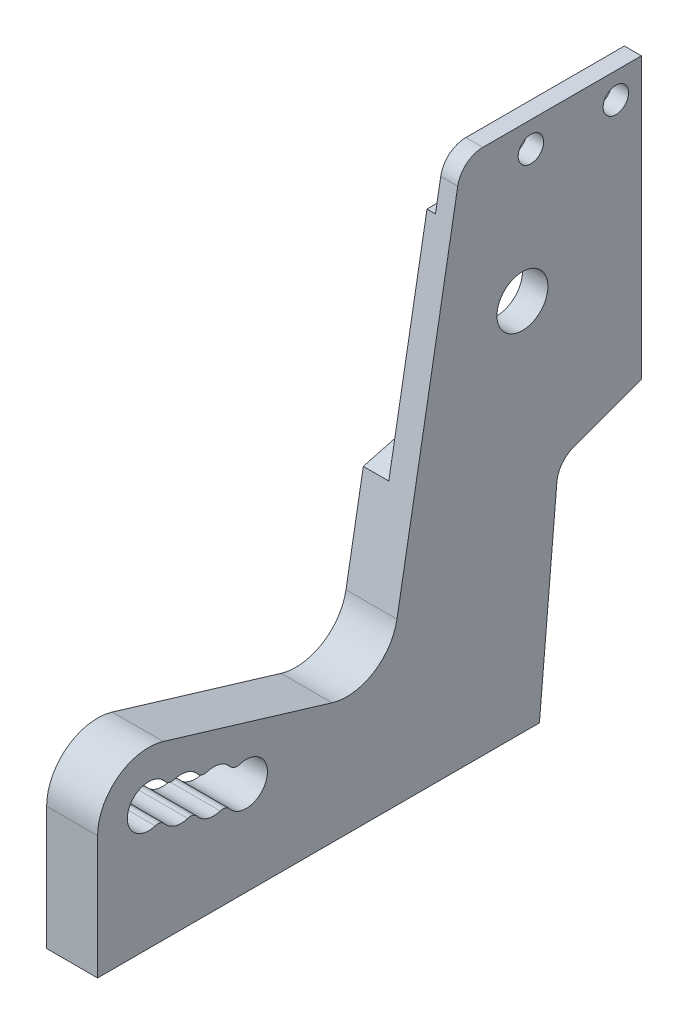
SolidWorks part; units mm, degrees
material "1060 Alloy"
ref_plane "Front Plane" through (0, 0, 0) normal (0, 0, 1) x (1, 0, 0)
ref_plane "Top Plane" through (0, 0, 0) normal (0, 1, 0) x (1, 0, 0)
ref_plane "Right Plane" through (0, 0, 0) normal (1, 0, 0) x (0, 0, -1)
sketch "Sketch1" plane through (0, 0, 0) normal (1, 0, 0) x (0, 0, -1)
  line L1 (0, 0) -> (64, 0)
  line L2 (0, 0) -> (0, 62)
  line L3 (0, 62) -> (64, 62)
  line L4 (64, 0) -> (64, 62)
  circle A0 centre (6, 14.5) radius 2.5
  circle A1 centre (50, 44) radius 3
  dimension "D1" = 6
  dimension "D2" = 5
  dimension "D3" = 14.5
  dimension "D4" = 6
  dimension "D5" = 44
  dimension "D6" = 50
  dimension "D7" = 64
  dimension "D8" = 62
extrude "Boss-Extrude1" add sketch "Sketch1" along normal blind 6
sketch "Sketch2" plane through (6, 0, 0) normal (1, 0, 0) x (0, 0, -1)
  line L0 (0, 62) -> (0, 0) construction
  line L1 (0, 0) -> (64, 0) construction
  line L2 (7.7322, 20.2445) -> (27.5931, 14.2555)
  line L4 (0, 14.5) -> (0, 63)
  line L5 (0, 63) -> (43, 63)
  line L6 (43, 63) -> (35.2342, 18.9581)
  line L7 (64, 62) -> (0, 62) construction
  arc A0 (0, 14.5) -> (7.7322, 20.2445) centre (6, 14.5) cw
  circle A1 centre (50, 44) radius 5 construction
  circle A2 centre (6, 14.5) radius 2.5 construction
  arc A4 (27.5931, 14.2555) -> (35.2342, 18.9581) centre (29.3254, 20) ccw
  dimension "D2" = 10
  dimension "D4" = 80
  dimension "D1" = 1
  dimension "D3" = 43
  dimension "D5" = 20
extrude "Cut-Extrude1" cut sketch "Sketch2" against normal up to next
sketch "Sketch3" plane through (6, 0, 0) normal (1, 0, 0) x (0, 0, -1)
  line L2 (0, 0) -> (64, 0) construction
  line L57 (64, 0) -> (52, 0)
  line L58 (64, 0) -> (64, 29)
  line L59 (64, 29) -> (54.2259, 25.4425)
  line L60 (52, 0) -> (54.2259, 25.4425)
  dimension "D1" = 52
  dimension "D2" = 29
  dimension "D3" = 70
  dimension "D4" = 85
extrude "Cut-Extrude2" cut sketch "Sketch3" against normal up to next
fillet "Fillet1" radius 3 1 edges at (3, 62, -42.8237)
fillet "Fillet2" radius 3 1 edges at (3, 25.4425, -54.2259)
hole_wizard "Tap Drill for M3 Tap1" positions "Sketch5" profile "Sketch4" hole size "M3" standard "ISO"
sketch "Sketch5" plane through (0, 0, 0) normal (0, -1, 0) x (-1, 0, 0)
  line L1 (-6, 0) -> (0, 0) construction
  line L2 (-6, 0) -> (-6, 52) construction
  point P0 (-3, 48)
  point P2 (-3, 12)
  dimension "D1" = 3
  dimension "D2" = 12
  dimension "D3" = 36
sketch "Sketch4" plane through (3, 0, -48) normal (1, 0, 0) x (0, 0, -1)
  line L0 (0, 0) -> (0, 9.7511)
  line L1 (0, 9.7511) -> (1.25, 9)
  line L2 (1.25, 9) -> (1.25, 0)
  line L5 (1.25, 0) -> (0, 0)
  line L10 (0, 9.7511) -> (-1.25, 9) construction
  line L11 (0, -6.35) -> (0, 107.95) construction
  dimension "Hole Dia." = 2.5
  dimension "Hole Depth" = 9
  dimension "Drill Angle" = 118
sketch "Sketch9" plane through (0, 0, 0) normal (-1, 0, 0) x (0, 0, 1)
  line L0 (-64, 62) -> (-64, 35)
  line L1 (-64, 62) -> (-45.341, 62) construction
  line L3 (-64, 29) -> (-64, 62) construction
  line L4 (-64, 62) -> (-42.8237, 62)
  line L5 (-42.8237, 62) -> (-37.2725, 30.5179)
  line L6 (-54, 35) -> (-64, 35)
  line L11 (-35.2342, 18.9581) -> (-42.3865, 59.5209) construction
  line L12 (-37.2725, 30.5179) -> (-54, 35)
  dimension "D1" = 10
  dimension "D2" = 27
  dimension "D5" = 65
extrude "Cut-Extrude3" cut sketch "Sketch9" against normal blind 3
sketch "Sketch10" plane through (3, 0, 0) normal (-1, 0, 0) x (0, 0, 1)
  line L0 (-45.341, 62) -> (-64, 62) construction
  line L1 (-64, 62) -> (-64, 35) construction
  circle A0 centre (-61, 59) radius 1.5
  circle A1 centre (-51, 59) radius 1.5
  dimension "D1" = 3
  dimension "D2" = 3
  dimension "D3" = 3
  dimension "D4" = 10
extrude "Cut-Extrude4" cut sketch "Sketch10" against normal up to next
sketch "Sketch11" plane through (0, 0, 0) normal (-1, 0, 0) x (0, 0, 1)
  line L0 (-6, 14.5) -> (-25.8609, 8.511) construction
  line L1 (-7.7322, 20.2445) -> (-27.5931, 14.2555) construction
  circle A0 centre (-9.8297, 13.3452) radius 2.5
  circle A1 centre (-6, 14.5) radius 2.5 construction
  dimension "D1" = 4
extrude "Cut-Extrude5" cut sketch "Sketch11" against normal up to next (6 mm away)
pattern_linear "LPattern1" count 3 spacing 4 along (0, -0.2887, -0.9574) of "Cut-Extrude5"
fillet "Fillet3" radius 1 6 edges at (3, 12.4865, -7.4818) (3, 15.3587, -8.3479) (3, 11.3316, -11.3114) (3, 14.2039, -12.1776) (3, 13.0491, -16.0072) (3, 10.1768, -15.1411)
sketch "Sketch12" plane through (3, 0, 0) normal (-1, 0, 0) x (0, 0, 1)
  line L1 (-64, 62) -> (-41.0174, 62)
  line L2 (-64, 62) -> (-64, 56)
  line L3 (-64, 56) -> (-41.0174, 56)
  line L4 (-41.0174, 62) -> (-41.0174, 56)
  dimension "D1" = 6
extrude "Cut-Extrude6" cut sketch "Sketch12" against normal blind 1
